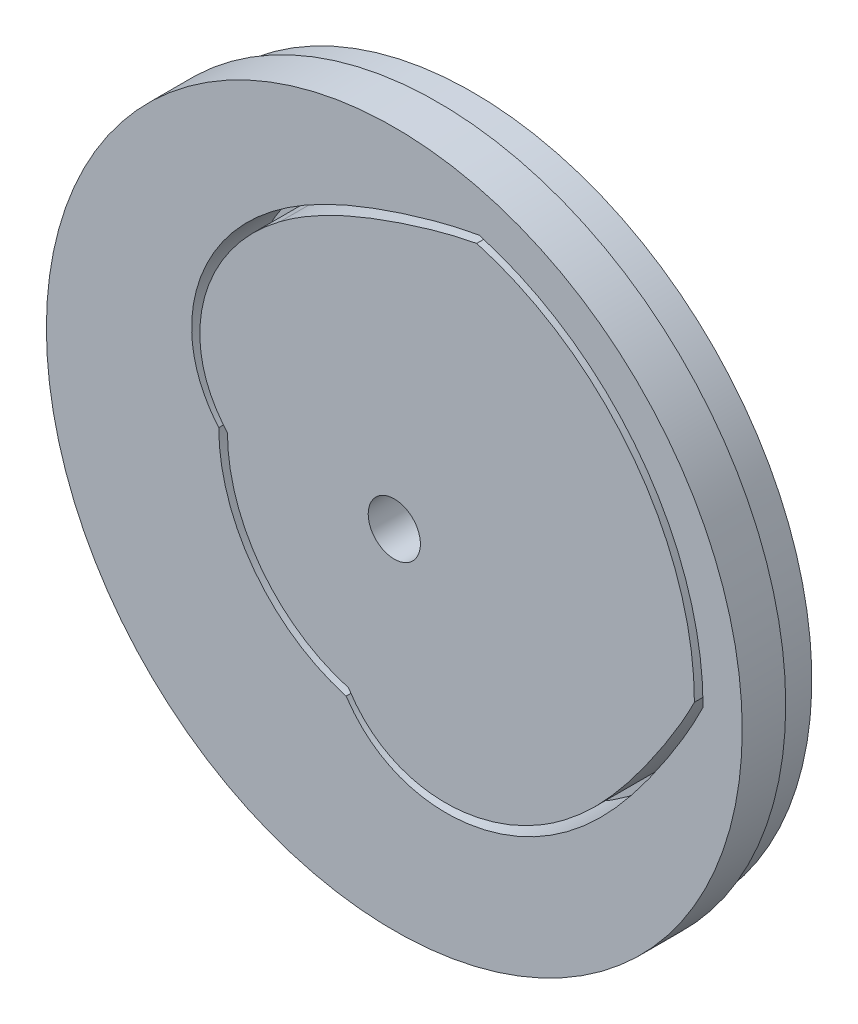
SolidWorks part; units mm, degrees
ref_plane "前视基准面" through (0, 0, 0) normal (0, 0, 1) x (1, 0, 0)
ref_plane "上视基准面" through (0, 0, 0) normal (0, 1, 0) x (1, 0, 0)
ref_plane "右视基准面" through (0, 0, 0) normal (1, 0, 0) x (0, 0, -1)
sketch "草图1" plane through (0, 0, 0) normal (0, 0, 1) x (1, 0, 0)
  circle A0 centre (0, 0) radius 36
extrude "凸台-拉伸1" add sketch "草图1" along normal blind 2
sketch "草图2" plane through (0, 0, 2) normal (0, 0, 1) x (1, 0, 0)
  circle A0 centre (0, 0) radius 30
extrude "凸台-拉伸2" add sketch "草图2" along normal blind 5
sketch "草图3" plane through (0, 0, 0) normal (0, 0, -1) x (-1, 0, 0)
  circle A0 centre (0, 0) radius 3
extrude "切除-拉伸1" cut sketch "草图3" against normal blind 25
sketch "草图4" plane through (0, 0, 0) normal (0, 0, -1) x (-1, 0, 0)
  circle A1 centre (0, 0) radius 39
extrude "凸台-拉伸3" add sketch "草图4" against normal up to surface (2 mm away) up to face at (36, 0, 2)
sketch "草图5" plane through (0, 0, 7) normal (0, 0, 1) x (1, 0, 0)
  circle A0 centre (0, 0) radius 40
extrude "凸台-拉伸4" add sketch "草图5" against normal up to surface (5 mm away) up to face at (30, 0, 2)
sketch "草图6" plane through (0, 0, 0) normal (0, 0, -1) x (-1, 0, 0)
  circle A0 centre (0, 0) radius 3
extrude "切除-拉伸2" cut sketch "草图6" against normal blind 10
sketch "草图7" plane through (0, 0, 0) normal (0, 0, -1) x (-1, 0, 0)
  circle A0 centre (0, 0) radius 39
extrude "凸台-拉伸5" add sketch "草图7" along normal blind 2
sketch "草图9" plane through (0, 0, 0) normal (0, 0, 1) x (1, 0, 0)
  arc A0 (9.7505, 34.1347) -> (35.5, 0) centre (0, 0) cw
  arc A1 (-5.5432, -19.4057) -> (-20.1819, 0) centre (0, 0) cw
  arc A2 (34.5001, 0) -> (9.4759, 33.1733) centre (0, 0) ccw
  arc A3 (-5.2684, -18.4442) -> (-19.1819, 0.0001) centre (0, 0) cw
  spline S0 degree 3 poles (9.7505, 34.1347) (9.2766, 34.0536) (8.5716, 33.92) (7.6408, 33.7225) (6.956, 33.5676) (6.2809, 33.4065) (5.6155, 33.24) (4.9597, 33.0689) (4.3132, 32.8938) (3.6759, 32.7154) (2.8421, 32.4741) (2.0207, 32.2288) (1.2125, 31.973) (0.6177, 31.7822) (0.0298, 31.5883) (-0.551, 31.3921) (-1.3126, 31.1285) (-2.0645, 30.8585) (-2.8067, 30.5817) (-3.3548, 30.3719) (-3.897, 30.1589) (-4.4334, 29.9425) (-4.9641, 29.7224) (-5.4893, 29.4985) (-6.0089, 29.2707) (-6.6926, 28.9621) (-7.3675, 28.6439) (-8.0332, 28.3154) (-8.5258, 28.0648) (-9.0131, 27.8091) (-9.4949, 27.5482) (-10.1288, 27.1939) (-10.9076, 26.7374) (-11.6701, 26.2603) (-12.2682, 25.867) (-12.71, 25.5666) (-13.1456, 25.2602) (-13.575, 24.9478) (-13.998, 24.6292) (-14.4145, 24.3046) (-14.8243, 23.9739) (-15.2271, 23.6369) (-15.6231, 23.294) (-16.1407, 22.8289) (-16.8942, 22.114) (-17.6119, 21.3658) (-18.4088, 20.4665) (-18.9498, 19.8044) (-19.4609, 19.1221) (-19.7573, 18.7081) (-20.044, 18.2887) (-20.3207, 17.8639) (-20.5872, 17.434) (-20.928, 16.8548) (-21.2478, 16.2651) (-21.545, 15.6657) (-21.756, 15.2122) (-21.955, 14.7546) (-22.1417, 14.293) (-22.3158, 13.8276) (-22.477, 13.3587) (-22.6248, 12.8865) (-22.7591, 12.4113) (-22.8793, 11.9334) (-22.9853, 11.4531) (-23.0765, 10.9707) (-23.1527, 10.4864) (-23.3141, 9.1972) (-23.329, 7.8862) (-23.1769, 6.5978) (-23.1019, 6.1168) (-23.0086, 5.6389) (-22.8969, 5.1646) (-22.7668, 4.6945) (-22.6181, 4.2294) (-22.4509, 3.7698) (-22.2654, 3.3166) (-22.0619, 2.8703) (-21.8406, 2.4318) (-21.6023, 2.0016) (-21.3475, 1.5806) (-21.0772, 1.1693) (-20.6977, 0.6352) (-20.3926, 0.2502) (-20.1819, 0) knots 0 0 0 0 0.026564 0.03964 0.052572 0.065355 0.077988 0.090471 0.102806 0.114993 0.127038 0.150763 0.162357 0.173876 0.185276 0.196564 0.207745 0.229808 0.240702 0.25151 0.262237 0.272889 0.283468 0.29398 0.304429 0.314817 0.335425 0.345652 0.355831 0.365965 0.376055 0.386104 0.406086 0.425925 0.435796 0.445634 0.455443 0.465223 0.474974 0.484699 0.494396 0.504069 0.513716 0.523338 0.542512 0.571097 0.580582 0.608903 0.618302 0.627679 0.637036 0.646371 0.655685 0.664979 0.683502 0.692733 0.701943 0.711133 0.720303 0.729453 0.738584 0.747695 0.756788 0.765863 0.77492 0.783961 0.792987 0.801998 0.855761 0.864721 0.873682 0.882647 0.891618 0.900599 0.90959 0.918594 0.927611 0.936643 0.945687 0.954743 0.963806 0.972871 0.981931 1 1 1 1
  spline S1 degree 3 poles (35.5, 0) (35.2918, -0.4334) (34.9698, -1.0746) (34.5242, -1.9153) (34.1872, -2.5313) (33.8469, -3.1361) (33.504, -3.7302) (33.1593, -4.3139) (32.8134, -4.8874) (32.4668, -5.4512) (32.0058, -6.1866) (31.5443, -6.9091) (31.0764, -7.6159) (30.7295, -8.1354) (30.3816, -8.6475) (30.0335, -9.1521) (29.5708, -9.812) (29.1047, -10.4608) (28.6346, -11.0984) (28.2824, -11.5678) (27.9286, -12.0307) (27.5732, -12.487) (27.2158, -12.9369) (26.8564, -13.3803) (26.4945, -13.8173) (26.01, -14.39) (25.5187, -14.9516) (25.02, -15.5014) (24.6437, -15.9063) (24.264, -16.3045) (23.8808, -16.6962) (23.3661, -17.2084) (22.7132, -17.8318) (22.045, -18.434) (21.5026, -18.901) (21.0924, -19.2433) (20.6781, -19.5781) (20.2597, -19.9051) (19.8373, -20.2244) (19.4108, -20.5357) (18.9802, -20.8389) (18.5455, -21.1337) (18.107, -21.4202) (17.5177, -21.7902) (16.6233, -22.3183) (15.7068, -22.803) (14.6232, -23.3222) (13.8379, -23.6606) (13.0415, -23.9645) (12.562, -24.1359) (12.08, -24.2963) (11.5956, -24.4458) (11.109, -24.5839) (10.4585, -24.7525) (9.8036, -24.898) (9.1456, -25.0191) (8.6516, -25.0975) (8.1569, -25.1631) (7.6618, -25.2159) (7.1665, -25.2555) (6.6713, -25.2817) (6.1767, -25.2941) (5.6829, -25.2927) (5.1904, -25.2771) (4.6994, -25.247) (4.2105, -25.2022) (3.724, -25.1425) (2.44, -24.9436) (1.1753, -24.5978) (-0.0218, -24.0977) (-0.4636, -23.8935) (-0.8976, -23.6725) (-1.323, -23.4349) (-1.7392, -23.1806) (-2.1456, -22.9098) (-2.5416, -22.6229) (-2.9265, -22.32) (-3.2997, -22.0017) (-3.6606, -21.6686) (-4.0087, -21.3213) (-4.3435, -20.9606) (-4.6648, -20.5877) (-5.0741, -20.0762) (-5.3605, -19.677) (-5.5432, -19.4057) knots 0 0 0 0 0.026564 0.03964 0.052572 0.065355 0.077988 0.090471 0.102806 0.114993 0.127038 0.150763 0.162357 0.173876 0.185276 0.196564 0.207745 0.229808 0.240702 0.25151 0.262237 0.272889 0.283468 0.29398 0.304429 0.314817 0.335425 0.345652 0.355831 0.365965 0.376055 0.386104 0.406086 0.425925 0.435796 0.445634 0.455443 0.465223 0.474974 0.484699 0.494396 0.504069 0.513716 0.523338 0.542512 0.571097 0.580582 0.608903 0.618302 0.627679 0.637036 0.646371 0.655685 0.664979 0.683502 0.692733 0.701943 0.711133 0.720303 0.729453 0.738584 0.747695 0.756788 0.765863 0.77492 0.783961 0.792987 0.801998 0.855761 0.864721 0.873682 0.882647 0.891618 0.900599 0.90959 0.918594 0.927611 0.936643 0.945687 0.954743 0.963806 0.972871 0.981931 1 1 1 1
  spline S2 degree 3 poles (9.4759, 33.1733) (9.0139, 33.0887) (8.3268, 32.9505) (7.42, 32.7472) (6.7533, 32.5885) (6.0964, 32.4237) (5.4491, 32.254) (4.8115, 32.0799) (4.1834, 31.9023) (3.5645, 31.7215) (2.9544, 31.5383) (2.3525, 31.3517) (1.759, 31.1657) (0.9843, 30.9112) (0.2203, 30.6552) (-0.5332, 30.3923) (-1.2702, 30.1294) (-2.1754, 29.795) (-3.0675, 29.4493) (-3.7687, 29.1671) (-4.2868, 28.9532) (-4.7992, 28.736) (-5.473, 28.4428) (-6.3021, 28.0669) (-7.1182, 27.6754) (-7.7601, 27.3534) (-8.548, 26.9462) (-9.3223, 26.5213) (-10.0813, 26.0776) (-10.5293, 25.8072) (-10.9717, 25.5314) (-11.4085, 25.2502) (-11.8395, 24.9635) (-12.4055, 24.5743) (-12.8223, 24.273) (-13.0965, 24.0679) knots 0 0 0 0 0.057469 0.085748 0.113704 0.141329 0.16862 0.195576 0.2222 0.248495 0.274471 0.300136 0.325605 0.350577 0.39991 0.424193 0.448236 0.495655 0.542262 0.56529 0.588147 0.610844 0.63339 0.678062 0.722224 0.744133 0.765934 0.830744 0.852168 0.873509 0.894771 0.915957 0.93707 0.958113 1 1 1 1
  spline S3 degree 3 poles (-13.0965, 24.0679) (-13.369, 23.8641) (-13.7721, 23.5522) (-14.2982, 23.1233) (-14.6854, 22.7962) (-15.0659, 22.4634) (-15.4393, 22.1247) (-15.8056, 21.7801) (-16.1645, 21.4296) (-16.5159, 21.0734) (-16.8595, 20.7114) (-17.1952, 20.3437) (-17.5228, 19.9703) (-17.842, 19.5912) (-18.1527, 19.2067) (-18.4545, 18.8166) (-18.7474, 18.4212) (-19.031, 18.0205) (-19.3051, 17.6146) (-19.5695, 17.2037) (-19.8239, 16.7878) (-20.5504, 15.5357) (-21.16, 14.2145) (-21.6172, 12.8478) (-21.7557, 12.3915) (-21.881, 11.9325) (-21.9925, 11.4709) (-22.0901, 11.0071) (-22.1732, 10.5413) (-22.2416, 10.0738) (-22.2948, 9.6051) (-22.4455, 7.7401) (-22.2394, 5.8177) (-21.6349, 4.0455) (-21.4645, 3.604) (-21.2761, 3.1691) (-21.07, 2.7411) (-20.8465, 2.3209) (-20.6063, 1.9092) (-20.35, 1.5066) (-20.0785, 1.1138) (-19.6979, 0.6042) (-19.3924, 0.2378) (-19.1819, 0.0001) knots 0 0 0 0 0.036455 0.054604 0.072704 0.090755 0.108758 0.126715 0.144627 0.162494 0.180317 0.198097 0.215834 0.233529 0.251182 0.268793 0.286363 0.303893 0.321382 0.33883 0.356238 0.373606 0.493927 0.510986 0.528009 0.544998 0.561953 0.578877 0.59577 0.612636 0.629477 0.646296 0.813191 0.83005 0.84694 0.863863 0.880821 0.897813 0.914833 0.931876 0.94893 0.965981 1 1 1 1
  spline S4 degree 3 poles (19.5452, -19.2033) (19.2744, -19.4094) (18.8637, -19.7114) (18.3069, -20.0994) (17.886, -20.3819) (17.4615, -20.6563) (17.0332, -20.9223) (16.6012, -21.1799) (16.1657, -21.4287) (15.7267, -21.6687) (15.2842, -21.8997) (14.8384, -22.1215) (14.3894, -22.3339) (13.9372, -22.5368) (13.4821, -22.7299) (13.0242, -22.913) (12.5635, -23.086) (12.1003, -23.2487) (11.6348, -23.4008) (11.167, -23.5421) (10.6972, -23.6725) (9.2938, -24.0271) (7.856, -24.2504) (6.4162, -24.3146) (5.9395, -24.3225) (5.4637, -24.3169) (4.9892, -24.2974) (4.5164, -24.2637) (4.0457, -24.2157) (3.5775, -24.1531) (3.1121, -24.0756) (1.2774, -23.7082) (-0.5143, -22.982) (-2.0524, -21.914) (-2.4301, -21.6289) (-2.7966, -21.3282) (-3.1514, -21.0125) (-3.4941, -20.6823) (-3.824, -20.3382) (-4.1407, -19.9812) (-4.4439, -19.6122) (-4.8293, -19.1063) (-5.0977, -18.7119) (-5.2684, -18.4442) knots 0 0 0 0 0.036455 0.054604 0.072704 0.090755 0.108758 0.126715 0.144627 0.162494 0.180317 0.198097 0.215834 0.233529 0.251182 0.268793 0.286363 0.303893 0.321382 0.33883 0.356238 0.373606 0.493927 0.510986 0.528009 0.544998 0.561953 0.578877 0.59577 0.612636 0.629477 0.646296 0.813191 0.83005 0.84694 0.863863 0.880821 0.897813 0.914833 0.931876 0.94893 0.965981 1 1 1 1
  spline S5 degree 3 poles (34.5001, 0) (34.2919, -0.421) (33.9703, -1.0437) (33.5258, -1.8598) (33.19, -2.4572) (32.8512, -3.0437) (32.5102, -3.6194) (32.1677, -4.1847) (31.8244, -4.7399) (31.4806, -5.2853) (31.1368, -5.8216) (30.7921, -6.3491) (30.4502, -6.8687) (29.9927, -7.5437) (29.5367, -8.208) (29.0769, -8.8604) (28.6217, -9.4968) (28.0516, -10.2753) (27.4742, -11.0381) (27.0102, -11.6349) (26.6623, -12.0743) (26.3127, -12.5074) (25.8457, -13.0747) (25.2565, -13.7687) (24.6559, -14.4458) (24.17, -14.9746) (23.562, -15.6203) (22.9409, -16.2482) (22.3057, -16.8561) (21.9226, -17.2126) (21.536, -17.5623) (21.1456, -17.905) (20.7515, -18.2407) (20.2219, -18.678) (19.8176, -18.9961) (19.5452, -19.2033) knots 0 0 0 0 0.057469 0.085748 0.113704 0.141329 0.16862 0.195576 0.2222 0.248495 0.274471 0.300136 0.325605 0.350577 0.39991 0.424193 0.448236 0.495655 0.542262 0.56529 0.588147 0.610844 0.63339 0.678062 0.722224 0.744133 0.765934 0.830744 0.852168 0.873509 0.894771 0.915957 0.93707 0.958113 1 1 1 1
sketch "草图10" plane through (0, 0, 7) normal (0, 0, 1) x (1, 0, 0)
extrude "切除-拉伸3" cut sketch "草图9" along normal through all
sketch "草图11" plane through (0, 0, 7) normal (0, 0, 1) x (1, 0, 0)
  circle A0 centre (0, 0) radius 3
extrude "切除-拉伸4" cut sketch "草图11" against normal blind 10
